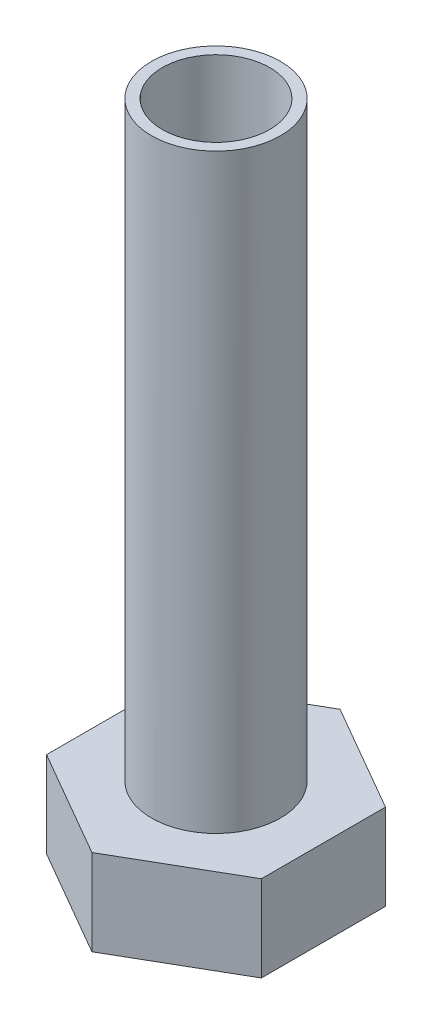
SolidWorks part; units mm, degrees
ref_plane "Front Plane" through (0, 0, 0) normal (0, 0, 1) x (1, 0, 0)
ref_plane "Top Plane" through (0, 0, 0) normal (0, 1, 0) x (1, 0, 0)
ref_plane "Right Plane" through (0, 0, 0) normal (1, 0, 0) x (0, 0, -1)
sketch "Sketch1" plane through (0, 0, 0) normal (0, 1, 0) x (1, 0, 0)
  circle A0 centre (0, 0) radius 3
  circle A1 centre (0, 0) radius 2.5
extrude "Boss-Extrude1" add sketch "Sketch1" along normal blind 27.5
sketch "Sketch2" plane through (0, 0, 0) normal (0, -1, 0) x (1, 0, 0)
  line L1 (0, 5.7735) -> (-5, 2.8868)
  line L2 (-5, 2.8868) -> (-5, -2.8868)
  line L3 (-5, -2.8868) -> (0, -5.7735)
  line L4 (0, -5.7735) -> (5, -2.8868)
  line L5 (5, -2.8868) -> (5, 2.8868)
  line L6 (5, 2.8868) -> (0, 5.7735)
  circle A0 centre (0, 0) radius 5 construction
extrude "Boss-Extrude2" add sketch "Sketch2" along normal blind 4
